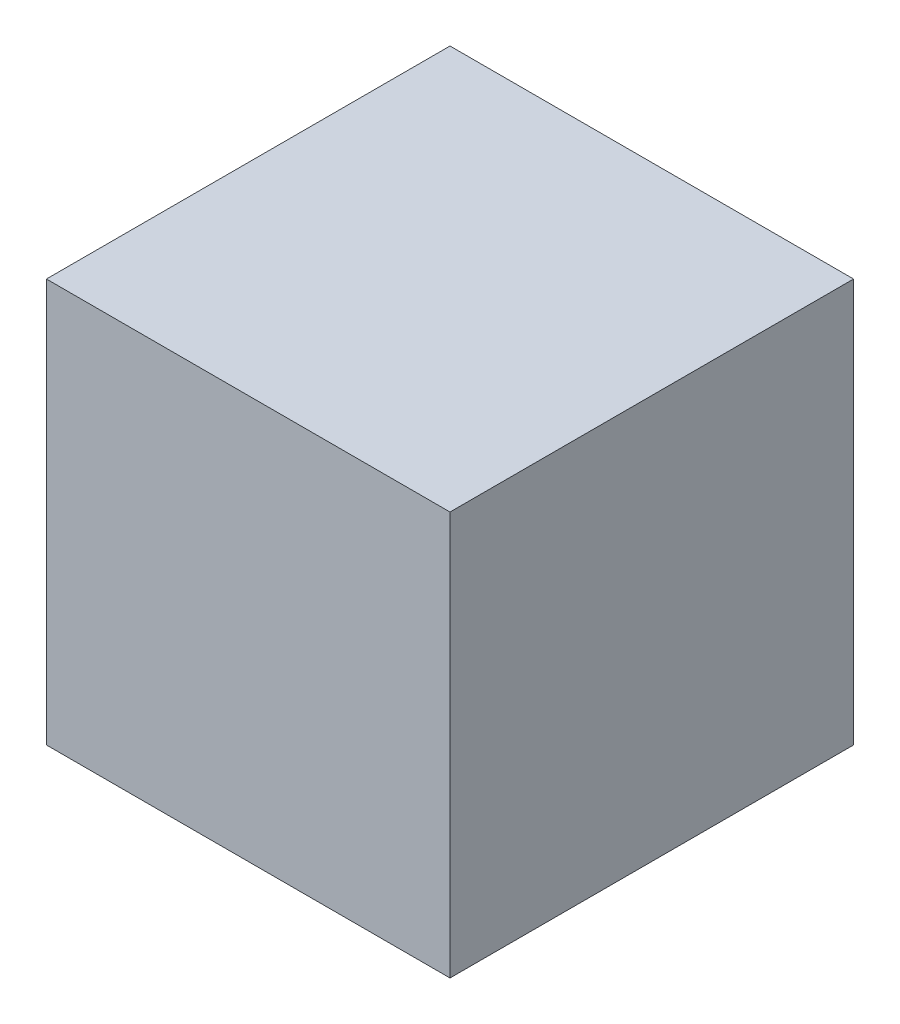
SolidWorks part; units mm, degrees
ref_plane "Front Plane" through (0, 0, 0) normal (0, 0, 1) x (1, 0, 0)
ref_plane "Top Plane" through (0, 0, 0) normal (0, 1, 0) x (1, 0, 0)
ref_plane "Right Plane" through (0, 0, 0) normal (1, 0, 0) x (0, 0, -1)
sketch "Sketch1" plane through (0, 0, 0) normal (0, 1, 0) x (1, 0, 0)
  line L1 (-25, 25) -> (25, 25)
  line L2 (-25, 25) -> (-25, -25)
  line L3 (-25, -25) -> (25, -25)
  line L4 (25, 25) -> (25, -25)
  point P4 (0, -25)
  point P6 (25, 0)
  dimension "D1" = 50
extrude "Boss-Extrude1" add sketch "Sketch1" along normal blind 50
